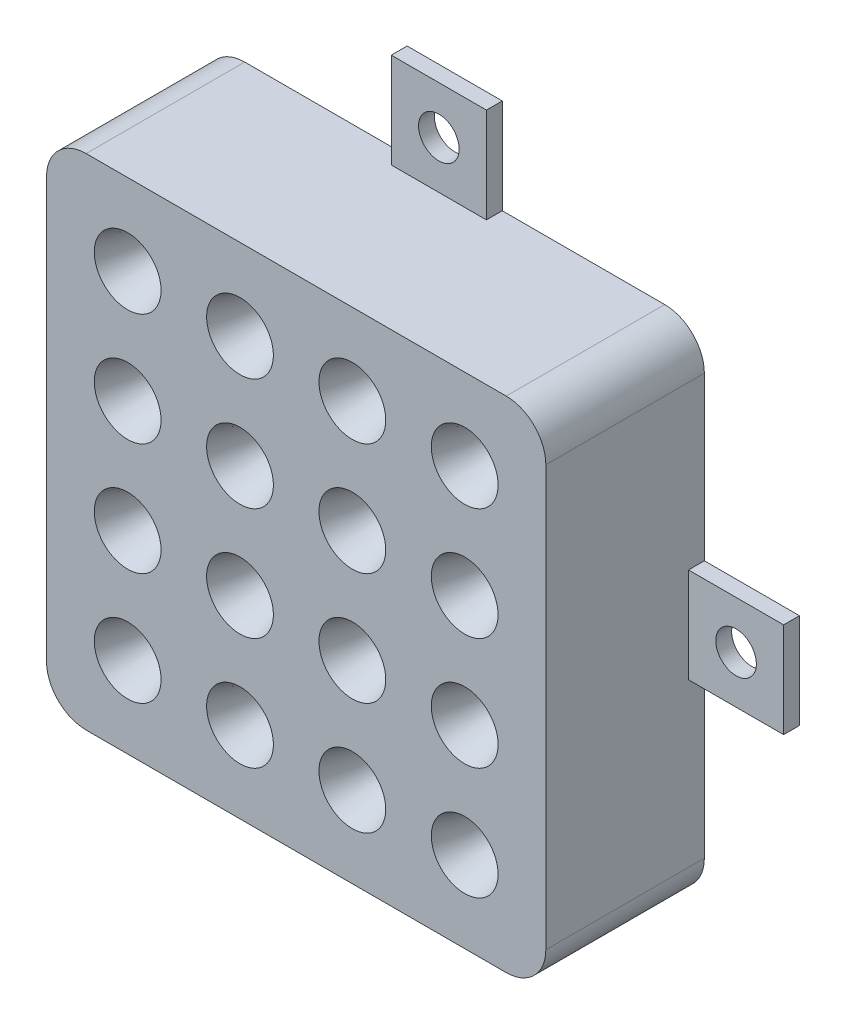
SolidWorks part; units mm, degrees
ref_plane "Front Plane" through (0, 0, 0) normal (0, 0, 1) x (1, 0, 0)
ref_plane "Top Plane" through (0, 0, 0) normal (0, 1, 0) x (1, 0, 0)
ref_plane "Right Plane" through (0, 0, 0) normal (1, 0, 0) x (0, 0, -1)
sketch "Sketch1" plane through (0, 0, 0) normal (0, 0, 1) x (1, 0, 0)
  line L1 (-52.4737, 14.5622) -> (-12.4737, 14.5622)
  line L2 (-52.4737, 14.5622) -> (-52.4737, -25.4378)
  line L3 (-52.4737, -25.4378) -> (-12.4737, -25.4378)
  line L4 (-12.4737, 14.5622) -> (-12.4737, -25.4378)
  dimension "D1" = 40
  dimension "D2" = 40
extrude "Boss-Extrude1" add sketch "Sketch1" along normal blind 12.7
sketch "Sketch2" plane through (0, 0, 12.7) normal (0, 0, 1) x (1, 0, 0)
  line L0 (-12.4737, 14.5622) -> (-52.4737, 14.5622) construction
  line L1 (-52.4737, 14.5622) -> (-52.4737, -25.4378) construction
  circle A0 centre (-45.9737, 8.0622) radius 2.6756
  circle A1 centre (-36.9737, 8.0622) radius 2.6756
  circle A2 centre (-27.9737, 8.0622) radius 2.6756
  circle A3 centre (-18.9737, 8.0622) radius 2.6756
  circle A4 centre (-45.9737, -0.9378) radius 2.6756
  circle A5 centre (-36.9737, -0.9378) radius 2.6756
  circle A6 centre (-27.9737, -0.9378) radius 2.6756
  circle A7 centre (-18.9737, -0.9378) radius 2.6756
  circle A8 centre (-45.9737, -9.9378) radius 2.6756
  circle A9 centre (-36.9737, -9.9378) radius 2.6756
  circle A10 centre (-27.9737, -9.9378) radius 2.6756
  circle A11 centre (-18.9737, -9.9378) radius 2.6756
  circle A12 centre (-45.9737, -18.9378) radius 2.6756
  circle A13 centre (-36.9737, -18.9378) radius 2.6756
  circle A14 centre (-27.9737, -18.9378) radius 2.6756
  circle A15 centre (-18.9737, -18.9378) radius 2.6756
  dimension "D1" = 5.3512
  dimension "D2" = 6.5
  dimension "D5" = 6.5
  dimension "D3" = 4
  dimension "D4" = 4
extrude "Cut-Extrude1" cut sketch "Sketch2" against normal blind 8 draft 17.5
fillet "Fillet1" radius 3.175 4 edges at (-52.4737, -25.4378, 6.35) (-52.4737, 14.5622, 6.35) (-12.4737, 14.5622, 6.35) (-12.4737, -25.4378, 6.35)
sketch "Sketch3" plane through (0, 14.5622, 0) normal (0, 1, 0) x (1, 0, 0)
  line L0 (-15.6487, 0) -> (-49.2987, 0) construction
  line L1 (-36.2837, 0) -> (-28.6637, 0)
  line L2 (-36.2837, 0) -> (-36.2837, -1.27)
  line L3 (-36.2837, -1.27) -> (-28.6637, -1.27)
  line L4 (-28.6637, 0) -> (-28.6637, -1.27)
  line L6 (-12.4737, 0) -> (-12.4737, -12.7) construction
  dimension "D1" = 1.27
  dimension "D2" = 7.62
  dimension "D3" = 16.19
extrude "Boss-Extrude2" add sketch "Sketch3" along normal blind 7.62
sketch "Sketch4" plane through (-12.4737, 0, 0) normal (1, 0, 0) x (0, 0, -1)
  line L0 (0, -22.2628) -> (0, 11.3872) construction
  line L1 (-1.27, -1.6278) -> (0, -1.6278)
  line L2 (-1.27, -1.6278) -> (-1.27, -9.2478)
  line L3 (-1.27, -9.2478) -> (0, -9.2478)
  line L4 (0, -1.6278) -> (0, -9.2478)
  line L5 (0, -25.4378) -> (-12.7, -25.4378) construction
  dimension "D1" = 7.62
  dimension "D2" = 16.19
  dimension "D3" = 1.27
extrude "Boss-Extrude3" add sketch "Sketch4" along normal blind 7.62
sketch "Sketch5" plane through (-52.4737, 0, 0) normal (-1, 0, 0) x (0, 0, 1)
  line L0 (0, 11.3872) -> (0, -22.2628) construction
  line L1 (1.27, -1.6277) -> (0, -1.6277)
  line L2 (1.27, -1.6277) -> (1.27, -9.2477)
  line L3 (1.27, -9.2477) -> (0, -9.2477)
  line L4 (0, -1.6277) -> (0, -9.2477)
  line L5 (0, 14.5622) -> (12.7, 14.5622) construction
  dimension "D1" = 16.19
  dimension "D2" = 7.62
  dimension "D3" = 1.27
extrude "Boss-Extrude4" add sketch "Sketch5" along normal blind 7.62
sketch "Sketch6" plane through (0, -25.4378, 0) normal (0, -1, 0) x (1, 0, 0)
  line L0 (-49.2987, 0) -> (-15.6487, 0) construction
  line L1 (-36.2838, 1.27) -> (-28.6638, 1.27)
  line L2 (-36.2838, 1.27) -> (-36.2838, 0)
  line L3 (-36.2838, 0) -> (-28.6638, 0)
  line L4 (-28.6638, 1.27) -> (-28.6638, 0)
  line L5 (-52.4737, 0) -> (-52.4737, 12.7) construction
  dimension "D1" = 7.62
  dimension "D2" = 16.19
  dimension "D3" = 1.27
extrude "Boss-Extrude5" add sketch "Sketch6" along normal blind 7.62
sketch "Sketch7" plane through (0, 0, 1.27) normal (0, 0, 1) x (1, 0, 0)
  line L0 (-28.6638, -33.0578) -> (-28.6638, -25.4378) construction
  line L1 (-28.6638, -33.0578) -> (-36.2838, -33.0578) construction
  line L2 (-60.0937, -9.2477) -> (-52.4737, -9.2477) construction
  line L3 (-60.0937, -9.2477) -> (-60.0937, -1.6277) construction
  line L4 (-4.8537, -9.2478) -> (-12.4737, -9.2478) construction
  line L5 (-4.8537, -1.6278) -> (-4.8537, -9.2478) construction
  line L6 (-36.2837, 22.1822) -> (-28.6637, 22.1822) construction
  line L7 (-28.6637, 22.1822) -> (-28.6637, 14.5622) construction
  circle A0 centre (-32.4738, -29.2478) radius 1.6256
  circle A1 centre (-56.2837, -5.4377) radius 1.6256
  circle A2 centre (-8.6637, -5.4378) radius 1.6256
  circle A3 centre (-32.4737, 18.3722) radius 1.6256
  dimension "D1" = 3.2512
  dimension "D4" = 3.2512
  dimension "D7" = 3.2512
  dimension "D10" = 3.81
  dimension "D12" = 3.2512
  dimension "D2" = 3.81
  dimension "D3" = 3.81
  dimension "D5" = 3.81
  dimension "D6" = 3.81
  dimension "D8" = 3.81
  dimension "D9" = 3.81
  dimension "D11" = 3.81
extrude "Cut-Extrude2" cut sketch "Sketch7" against normal blind 7.62 contours A0 | A2 | A1 | A3
